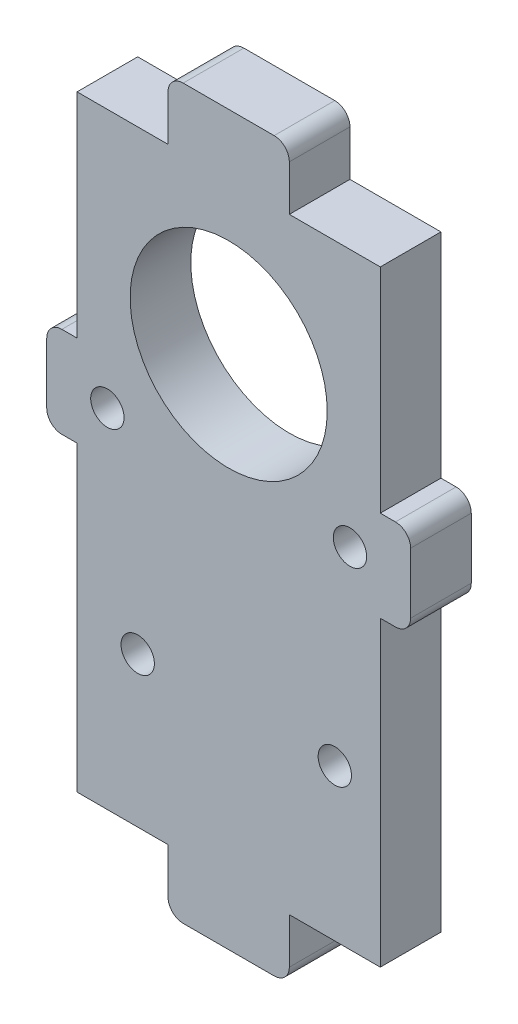
SolidWorks part; units mm, degrees
ref_plane "Front Plane" through (0, 0, 0) normal (0, 0, 1) x (1, 0, 0)
ref_plane "Top Plane" through (0, 0, 0) normal (0, 1, 0) x (1, 0, 0)
ref_plane "Right Plane" through (0, 0, 0) normal (1, 0, 0) x (0, 0, -1)
sketch "Sketch1" plane through (0, 0, 0) normal (0, 0, 1) x (1, 0, 0)
  line L0 (0, 20) -> (0, -20) construction
  line L1 (-10, 20) -> (10, 20)
  line L2 (-10, 20) -> (-10, -20)
  line L3 (-10, -20) -> (10, -20)
  line L4 (10, 20) -> (10, -20)
  line L5 (-10, 20) -> (10, -20) construction
  line L6 (-10, -20) -> (10, 20) construction
  line L7 (-16, 19.9337) -> (-16, -20.0663) construction
  line L8 (-10, 2.9337) -> (10, 2.9337) construction
  line L9 (-4, 20) -> (4, 20)
  line L10 (-4, 20) -> (-4, 23)
  line L11 (-3, 24) -> (3, 24)
  line L12 (4, 20) -> (4, 23)
  line L13 (-10, 5.9337) -> (-11, 5.9337)
  line L14 (-10, 5.9337) -> (-10, -0.0663)
  line L15 (-10, -0.0663) -> (-11, -0.0663)
  line L16 (-12, 4.9337) -> (-12, 0.9337)
  line L17 (10, 5.9337) -> (11, 5.9337)
  line L18 (10, 5.9337) -> (10, -0.0663)
  line L19 (10, -0.0663) -> (11, -0.0663)
  line L20 (12, 4.9337) -> (12, 0.9337)
  line L21 (-4, -20) -> (4, -20)
  line L22 (-4, -20) -> (-4, -23)
  line L23 (-3, -24) -> (3, -24)
  line L24 (4, -20) -> (4, -23)
  circle A0 centre (0, 10) radius 6.5
  circle A1 centre (8, 3) radius 1.1
  circle A2 centre (-8, 2.9337) radius 1.1
  circle A3 centre (-6, -10.1181) radius 1.1
  circle A4 centre (7, -10) radius 1.1
  arc A5 (3, 24) -> (4, 23) centre (3, 23) cw
  arc A6 (-4, 23) -> (-3, 24) centre (-3, 23) cw
  arc A7 (-4, -23) -> (-3, -24) centre (-3, -23) ccw
  arc A8 (3, -24) -> (4, -23) centre (3, -23) ccw
  arc A9 (11, -0.0663) -> (12, 0.9337) centre (11, 0.9337) ccw
  arc A10 (11, 5.9337) -> (12, 4.9337) centre (11, 4.9337) cw
  arc A11 (-11, -0.0663) -> (-12, 0.9337) centre (-11, 0.9337) cw
  arc A12 (-11, 5.9337) -> (-12, 4.9337) centre (-11, 4.9337) ccw
  point P0 (0, 0)
  point P40 (4, 24)
  point P47 (4, -24)
  point P50 (12, -0.0663)
  point P53 (12, 5.9337)
  point P56 (-12, -0.0663)
  point P59 (-12, 5.9337)
  dimension "D4" = 13
  dimension "D5" = 2.2
  dimension "D9" = 2.2
  dimension "D22" = 1
  dimension "D1" = 20
  dimension "D2" = 40
  dimension "D3" = 10
  dimension "D6" = 17
  dimension "D7" = 2
  dimension "D10" = 4
  dimension "D12" = 4
  dimension "D13" = 4
  dimension "D14" = 2
  dimension "D15" = 2
  dimension "D16" = 4
  dimension "D17" = 4
  dimension "D18" = 6
  dimension "D19" = 6
  dimension "D20" = 3
  dimension "D21" = 3
  dimension "D23" = 16
  dimension "D24" = 7
  dimension "D25" = 30
  dimension "D26" = 4
  dimension "D27" = 4
  dimension "D8" = 2
  dimension "D11" = 2
extrude "Boss-Extrude2" add sketch "Sketch1" along normal blind 4 contours L4 L1 L2 L3 A4 A3 A2 A1 A0 | A6 L10 L1 L12 A5 L11 | A10 L17 L4 L19 A9 L20 | L23 A8 L24 L3 L22 A7 | L13 A12 L16 A11 L15 L2
